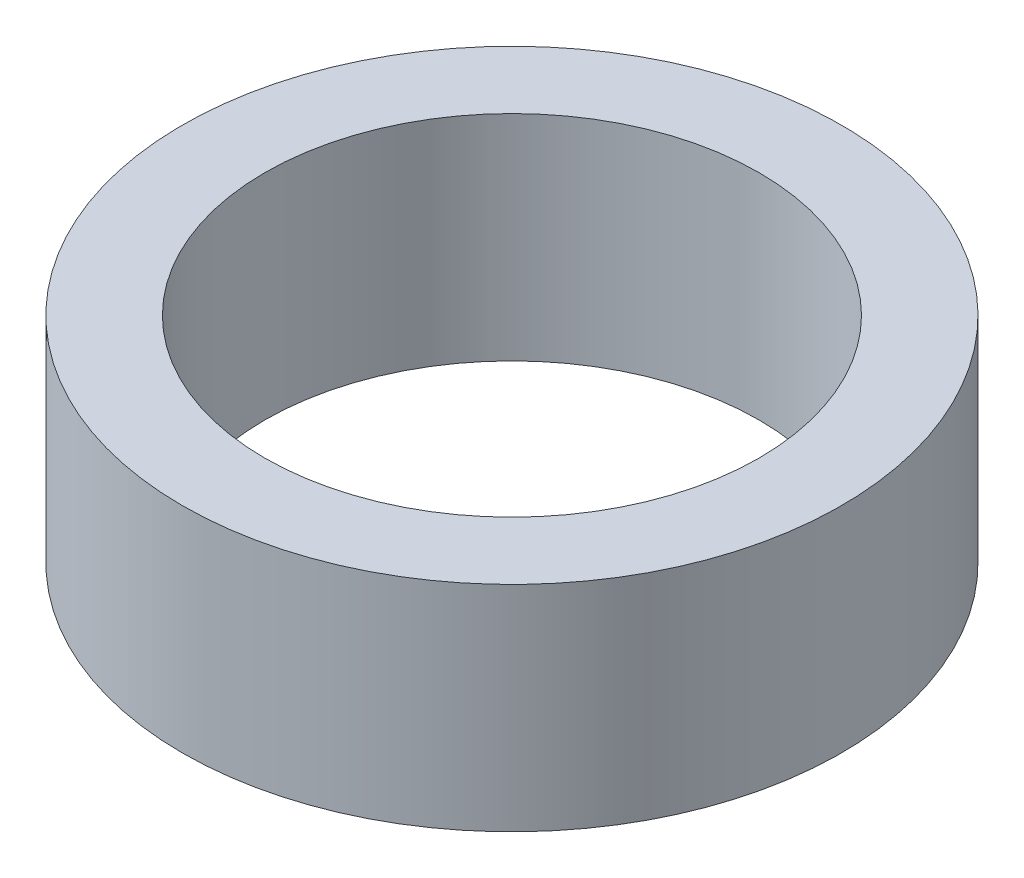
SolidWorks part; units mm, degrees
material "AISI 304"
ref_plane "前视基准面" through (0, 0, 0) normal (0, 0, 1) x (1, 0, 0)
ref_plane "上视基准面" through (0, 0, 0) normal (0, 1, 0) x (1, 0, 0)
ref_plane "右视基准面" through (0, 0, 0) normal (1, 0, 0) x (0, 0, -1)
sketch "Sketch1" plane through (0, 0, 0) normal (0, 1, 0) x (1, 0, 0)
  circle A0 centre (0, 0) radius 15
  circle A1 centre (0, 0) radius 20
  dimension "D1" = 30
  dimension "D2" = 40
extrude "Boss-Extrude1" add sketch "Sketch1" along normal mid plane 13
